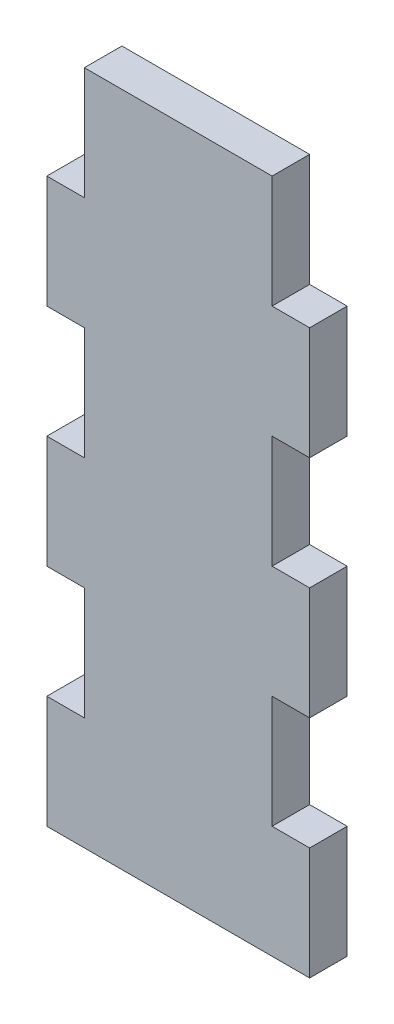
SolidWorks part; units mm, degrees
ref_plane "Front Plane" through (0, 0, 0) normal (0, 0, 1) x (1, 0, 0)
ref_plane "Top Plane" through (0, 0, 0) normal (0, 1, 0) x (1, 0, 0)
ref_plane "Right Plane" through (0, 0, 0) normal (1, 0, 0) x (0, 0, -1)
sketch "Model" plane through (0, 0, 0) normal (0, 0, 1) x (1, 0, 0)
  line L0 (25.4994, 117.749) -> (25.4994, 99.749)
  line L1 (25.4994, 99.749) -> (19.4994, 99.749)
  line L2 (19.4994, 99.749) -> (19.4994, 81.749)
  line L3 (25.4994, 81.749) -> (25.4994, 63.749)
  line L4 (25.4994, 63.749) -> (19.4994, 63.749)
  line L5 (19.4994, 63.749) -> (19.4994, 45.749)
  line L6 (25.4994, 45.749) -> (25.4994, 27.749)
  line L7 (25.4994, 27.749) -> (19.4994, 27.749)
  line L8 (19.4994, 27.749) -> (19.4994, 9.749)
  line L9 (25.4994, 81.749) -> (19.4994, 81.749)
  line L10 (19.4994, 45.749) -> (25.4994, 45.749)
  line L11 (55.4994, 117.749) -> (55.4994, 99.749)
  line L12 (55.4994, 99.749) -> (61.4994, 99.749)
  line L13 (61.4994, 99.749) -> (61.4994, 81.749)
  line L14 (55.4994, 81.749) -> (55.4994, 63.749)
  line L15 (55.4994, 63.749) -> (61.4994, 63.749)
  line L16 (61.4994, 63.749) -> (61.4994, 45.749)
  line L17 (55.4994, 45.749) -> (55.4994, 27.749)
  line L18 (55.4994, 27.749) -> (61.4994, 27.749)
  line L19 (61.4994, 27.749) -> (61.4994, 9.749)
  line L20 (55.4994, 81.749) -> (61.4994, 81.749)
  line L21 (61.4994, 45.749) -> (55.4994, 45.749)
  line L22 (25.4994, 117.749) -> (55.4994, 117.749)
  line L23 (19.4994, 9.749) -> (61.4994, 9.749)
extrude "Boss-Extrude1" add sketch "Model" along normal blind 6 contours L5 L10 L6 L7 L8 L23 L19 L18 L17 L21 L16 L15 L14 L20 L13 L12 L11 L22 L0 L1 L2 L9 L3 L4
